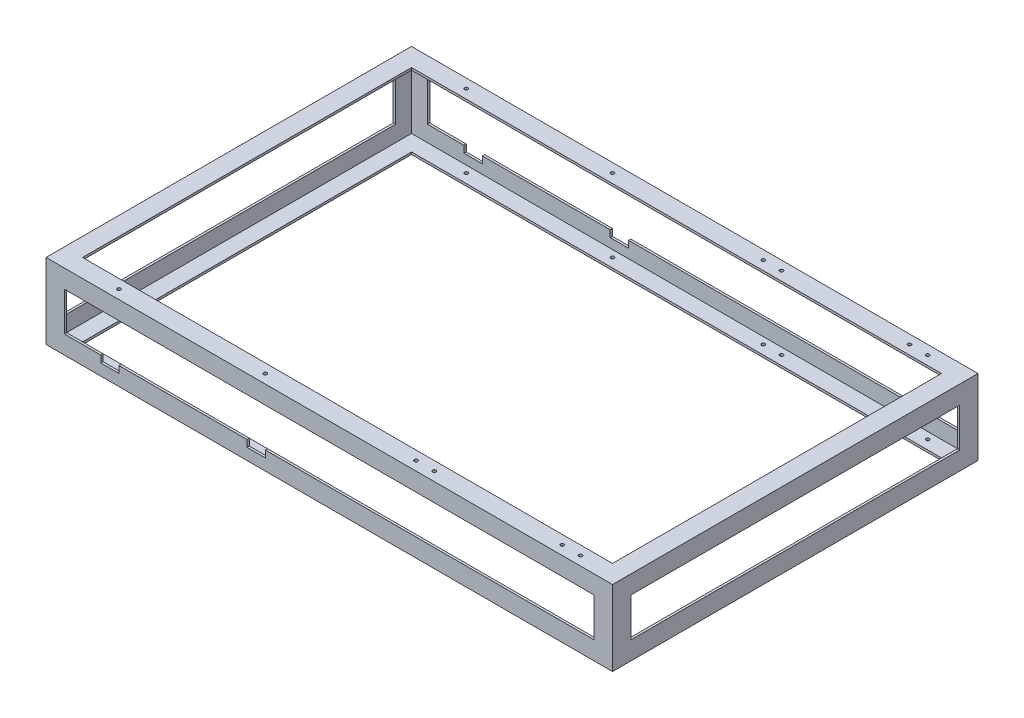
SolidWorks part; units mm, degrees
material "6061 Alloy"
ref_plane "Front Plane" through (0, 0, 0) normal (0, 0, 1) x (1, 0, 0)
ref_plane "Top Plane" through (0, 0, 0) normal (0, 1, 0) x (1, 0, 0)
ref_plane "Right Plane" through (0, 0, 0) normal (1, 0, 0) x (0, 0, -1)
other "Center of Mass"
sketch "Sketch2" plane through (0, 0, 0) normal (1, 0, 0) x (0, 0, -1)
  line L0 (-504.825, -346.075) -> (-504.825, -422.275)
  line L1 (504.825, -422.275) -> (-504.825, -422.275) construction
  line L2 (504.825, -422.275) -> (504.825, 422.275) construction
  line L3 (504.825, 422.275) -> (-504.825, 422.275) construction
  line L4 (-504.825, -422.275) -> (-504.825, 422.275) construction
  line L5 (504.825, -422.275) -> (-504.825, 422.275) construction
  line L6 (504.825, 422.275) -> (-504.825, -422.275) construction
  line L7 (-504.825, -422.275) -> (-428.625, -422.275)
  line L8 (-428.625, -422.275) -> (-428.625, -417.195)
  line L9 (-428.625, -417.195) -> (-498.7519, -417.195)
  line L10 (-498.7519, -417.195) -> (-498.7519, -346.075)
  line L11 (-498.7519, -346.075) -> (-504.825, -346.075)
  line L12 (0, 0) -> (0, -148.4726) construction
  line L13 (0, 0) -> (158.633, 0) construction
  line L14 (498.7519, -417.195) -> (498.7519, -346.075)
  line L15 (428.625, -417.195) -> (498.7519, -417.195)
  line L16 (428.625, -422.275) -> (428.625, -417.195)
  line L17 (504.825, -422.275) -> (428.625, -422.275)
  line L18 (504.825, -346.075) -> (504.825, -422.275)
  line L19 (498.7519, -346.075) -> (504.825, -346.075)
  line L20 (428.625, 417.195) -> (498.7519, 417.195)
  line L21 (428.625, 422.275) -> (428.625, 417.195)
  line L22 (504.825, 422.275) -> (428.625, 422.275)
  line L23 (504.825, 346.075) -> (504.825, 422.275)
  line L24 (498.7519, 346.075) -> (504.825, 346.075)
  line L25 (498.7519, 417.195) -> (498.7519, 346.075)
  line L26 (-498.7519, 417.195) -> (-498.7519, 346.075)
  line L27 (-428.625, 417.195) -> (-498.7519, 417.195)
  line L28 (-428.625, 422.275) -> (-428.625, 417.195)
  line L29 (-504.825, 422.275) -> (-428.625, 422.275)
  line L30 (-504.825, 346.075) -> (-504.825, 422.275)
  line L31 (-498.7519, 346.075) -> (-504.825, 346.075)
  point P0 (0, 0)
  dimension "D1" = 1009.65
  dimension "D2" = 844.55
  dimension "D3" = 76.2
  dimension "D4" = 5.08
extrude "OAL Lenth" [suppressed] add sketch "Sketch2" along normal blind 1574.8
sketch "Sketch3" [suppressed] plane through (0, 0, 0) normal (0, 0, 1) x (1, 0, 0)
  line L0 (0, -422.275) -> (0, -346.075)
  line L1 (1574.8, -346.075) -> (0, -346.075) construction
  line L2 (0, -346.075) -> (0, -422.275) construction
  line L3 (0, -346.075) -> (5.08, -346.075)
  line L4 (5.08, -346.075) -> (5.08, -417.195)
  line L5 (5.08, -417.195) -> (76.2, -417.195)
  line L6 (76.2, -417.195) -> (76.2, -422.275)
  line L7 (1574.8, -422.275) -> (0, -422.275) construction
  line L8 (76.2, -422.275) -> (0, -422.275)
  line L9 (0, 0) -> (697.1877, 0) construction
  line L10 (787.4, 346.075) -> (787.4, -346.075) construction
  line L11 (1574.8, 346.075) -> (0, 346.075) construction
  line L12 (76.2, 422.275) -> (0, 422.275)
  line L13 (76.2, 417.195) -> (76.2, 422.275)
  line L14 (5.08, 417.195) -> (76.2, 417.195)
  line L15 (5.08, 346.075) -> (5.08, 417.195)
  line L16 (0, 346.075) -> (5.08, 346.075)
  line L17 (0, 422.275) -> (0, 346.075)
  line L18 (1574.8, 422.275) -> (1574.8, 346.075)
  line L19 (1574.8, 346.075) -> (1569.72, 346.075)
  line L20 (1569.72, 346.075) -> (1569.72, 417.195)
  line L21 (1569.72, 417.195) -> (1498.6, 417.195)
  line L22 (1498.6, 417.195) -> (1498.6, 422.275)
  line L23 (1498.6, 422.275) -> (1574.8, 422.275)
  line L24 (1498.6, -422.275) -> (1574.8, -422.275)
  line L25 (1498.6, -417.195) -> (1498.6, -422.275)
  line L26 (1569.72, -417.195) -> (1498.6, -417.195)
  line L27 (1569.72, -346.075) -> (1569.72, -417.195)
  line L28 (1574.8, -346.075) -> (1569.72, -346.075)
  line L29 (1574.8, -422.275) -> (1574.8, -346.075)
  dimension "D1" = 5.08
extrude "OAL Width" [suppressed] add sketch "Sketch3" along normal up to surface and the other way up to surface
sketch "Sketch4" [suppressed] plane through (0, 422.275, 0) normal (0, 1, 0) x (1, 0, 0)
  line L0 (0, 504.825) -> (0, 428.625)
  line L1 (0, -428.625) -> (0, -504.825) construction
  line L2 (0, 428.625) -> (5.08, 428.625)
  line L3 (5.08, 428.625) -> (5.08, 499.745)
  line L4 (5.08, 499.745) -> (76.2, 499.745)
  line L5 (76.2, 499.745) -> (76.2, 504.825)
  line L6 (0, 504.825) -> (1574.8, 504.825) construction
  line L7 (76.2, 504.825) -> (0, 504.825)
  line L8 (0, 0) -> (1574.8, 0) construction
  line L9 (1574.8, -428.625) -> (1574.8, -504.825) construction
  line L10 (787.4, 0) -> (787.4, 504.825) construction
  line L11 (76.2, -504.825) -> (0, -504.825)
  line L12 (76.2, -499.745) -> (76.2, -504.825)
  line L13 (5.08, -499.745) -> (76.2, -499.745)
  line L14 (5.08, -428.625) -> (5.08, -499.745)
  line L15 (0, -428.625) -> (5.08, -428.625)
  line L16 (0, -504.825) -> (0, -428.625)
  line L17 (1574.8, -504.825) -> (1574.8, -428.625)
  line L18 (1574.8, -428.625) -> (1569.72, -428.625)
  line L19 (1569.72, -428.625) -> (1569.72, -499.745)
  line L20 (1569.72, -499.745) -> (1498.6, -499.745)
  line L21 (1498.6, -499.745) -> (1498.6, -504.825)
  line L22 (1498.6, -504.825) -> (1574.8, -504.825)
  line L23 (1498.6, 504.825) -> (1574.8, 504.825)
  line L24 (1498.6, 499.745) -> (1498.6, 504.825)
  line L25 (1569.72, 499.745) -> (1498.6, 499.745)
  line L26 (1569.72, 428.625) -> (1569.72, 499.745)
  line L27 (1574.8, 428.625) -> (1569.72, 428.625)
  line L28 (1574.8, 504.825) -> (1574.8, 428.625)
  dimension "D1" = 5.08
  dimension "D2" = 76.2
extrude "OAL Height" [suppressed] add sketch "Sketch4" against normal through all
sketch "Sketch5" plane through (0, 0, 0) normal (1, 0, 0) x (0, 0, -1)
  line L0 (0, 304.8) -> (0, -304.8) construction
  line L1 (-508, -304.8) -> (508, -304.8) construction
  line L2 (-508, -304.8) -> (-508, -254)
  line L3 (-508, -304.8) -> (-457.2, -304.8)
  line L4 (-457.2, -304.8) -> (-457.2, -298.45)
  line L5 (-457.2, -298.45) -> (-501.65, -298.45)
  line L6 (-501.65, -298.45) -> (-501.65, -254)
  line L7 (-501.65, -254) -> (-508, -254)
  line L8 (501.65, -254) -> (508, -254)
  line L9 (501.65, -298.45) -> (501.65, -254)
  line L10 (457.2, -298.45) -> (501.65, -298.45)
  line L11 (457.2, -304.8) -> (457.2, -298.45)
  line L12 (508, -304.8) -> (457.2, -304.8)
  line L13 (508, -304.8) -> (508, -254)
  line L14 (0, -200.025) -> (-176.3903, -200.025) construction
  line L15 (-508, -95.25) -> (508, -95.25) construction
  line L16 (508, -95.25) -> (508, -146.05)
  line L17 (508, -95.25) -> (457.2, -95.25)
  line L18 (457.2, -95.25) -> (457.2, -101.6)
  line L19 (457.2, -101.6) -> (501.65, -101.6)
  line L20 (501.65, -101.6) -> (501.65, -146.05)
  line L21 (501.65, -146.05) -> (508, -146.05)
  line L22 (-501.65, -146.05) -> (-508, -146.05)
  line L23 (-501.65, -101.6) -> (-501.65, -146.05)
  line L24 (-457.2, -101.6) -> (-501.65, -101.6)
  line L25 (-457.2, -95.25) -> (-457.2, -101.6)
  line L26 (-508, -95.25) -> (-457.2, -95.25)
  line L27 (-508, -95.25) -> (-508, -146.05)
  point P4 (0, 0)
  point P8 (0, -304.8)
  point P32 (0, -95.25)
  dimension "D1" = 1016
  dimension "D2" = 609.6
  dimension "D3" = 50.8
  dimension "D4" = 6.35
  dimension "D5" = 104.775
extrude "X Angle Lenth" add sketch "Sketch5" along normal blind 1574.8 separate body
sketch "Sketch6" plane through (0, -304.8, 0) normal (0, -1, 0) x (1, 0, 0)
  line L0 (0, 0) -> (1574.8, 0) construction
  line L1 (1574.8, -508) -> (1574.8, 508) construction
  line L2 (1574.8, -508) -> (1524, -508)
  line L3 (1574.8, -508) -> (1574.8, -457.2)
  line L4 (1574.8, -457.2) -> (1568.45, -457.2)
  line L5 (1568.45, -457.2) -> (1568.45, -501.65)
  line L6 (1568.45, -501.65) -> (1524, -501.65)
  line L7 (1524, -501.65) -> (1524, -508)
  line L8 (1524, 501.65) -> (1524, 508)
  line L9 (1568.45, 501.65) -> (1524, 501.65)
  line L10 (1568.45, 457.2) -> (1568.45, 501.65)
  line L11 (1574.8, 457.2) -> (1568.45, 457.2)
  line L12 (1574.8, 508) -> (1574.8, 457.2)
  line L13 (1574.8, 508) -> (1524, 508)
  line L15 (787.4, 0) -> (787.4, 197.6325) construction
  line L16 (0, -508) -> (0, 508) construction
  line L17 (0, 508) -> (50.8, 508)
  line L18 (0, 508) -> (0, 457.2)
  line L19 (0, 457.2) -> (6.35, 457.2)
  line L20 (6.35, 457.2) -> (6.35, 501.65)
  line L21 (6.35, 501.65) -> (50.8, 501.65)
  line L22 (50.8, 501.65) -> (50.8, 508)
  line L23 (50.8, -501.65) -> (50.8, -508)
  line L24 (6.35, -501.65) -> (50.8, -501.65)
  line L25 (6.35, -457.2) -> (6.35, -501.65)
  line L26 (0, -457.2) -> (6.35, -457.2)
  line L27 (0, -508) -> (0, -457.2)
  line L28 (0, -508) -> (50.8, -508)
  point P3 (787.4, 0)
  point P6 (1574.8, 0)
  point P32 (0, 0)
  dimension "D1" = 50.8
  dimension "D2" = 6.35
  dimension "D3" = 1016
  dimension "D4" = 1574.8
extrude "Y Angle Lenth" add sketch "Sketch6" against normal blind 209.55
sketch "Sketch15" plane through (0, 0, 0) normal (0, 0, 1) x (1, 0, 0)
  line L0 (0, -254) -> (0, -304.8)
  line L1 (0, -95.25) -> (1574.8, -95.25) construction
  line L2 (787.4, -95.25) -> (787.4, 43.9233) construction
  line L3 (1568.45, -254) -> (1574.8, -254)
  line L4 (1568.45, -298.45) -> (1568.45, -254)
  line L5 (1524, -298.45) -> (1568.45, -298.45)
  line L6 (1524, -304.8) -> (1524, -298.45)
  line L7 (0, -304.8) -> (50.8, -304.8)
  line L8 (50.8, -304.8) -> (50.8, -298.45)
  line L9 (50.8, -298.45) -> (6.35, -298.45)
  line L10 (6.35, -298.45) -> (6.35, -254)
  line L11 (6.35, -254) -> (0, -254)
  line L12 (1574.8, -304.8) -> (1524, -304.8)
  line L13 (1574.8, -254) -> (1574.8, -304.8)
  line L20 (787.4, -95.25) -> (787.4, -304.8) construction
  line L21 (1574.8, -304.8) -> (0, -304.8) construction
  line L24 (787.4, -200.025) -> (896.4031, -200.025) construction
  line L27 (1574.8, -146.05) -> (1574.8, -95.25)
  line L28 (1574.8, -95.25) -> (1524, -95.25)
  line L29 (1524, -95.25) -> (1524, -101.6)
  line L30 (1524, -101.6) -> (1568.45, -101.6)
  line L31 (1568.45, -101.6) -> (1568.45, -146.05)
  line L32 (1568.45, -146.05) -> (1574.8, -146.05)
  line L33 (18.8814, -200.025) -> (113.1502, -200.025) construction
  line L35 (6.35, -146.05) -> (0, -146.05)
  line L36 (6.35, -101.6) -> (6.35, -146.05)
  line L37 (50.8, -101.6) -> (6.35, -101.6)
  line L38 (50.8, -95.25) -> (50.8, -101.6)
  line L39 (0, -95.25) -> (50.8, -95.25)
  line L40 (0, -146.05) -> (0, -95.25)
  dimension "D1" = 50.8
  dimension "D2" = 6.35
extrude "Z Angle Lenth" add sketch "Sketch15" against normal up to surface and the other way up to surface
sketch "Sketch16" plane through (0, -95.25, 0) normal (0, 1, 0) x (1, 0, 0)
  line L0 (1409.7, 0) -> (1409.7, 482.6) construction
  line L1 (0, 508) -> (0, -508) construction
  line L2 (1003.3, 0) -> (1003.3, 482.6) construction
  line L3 (584.2, 0) -> (584.2, 482.6) construction
  line L4 (177.8, 0) -> (177.8, 482.6) construction
  line L5 (177.8, 482.6) -> (584.2, 482.6) construction
  line L6 (584.2, 482.6) -> (1003.3, 482.6) construction
  line L7 (1003.3, 482.6) -> (1409.7, 482.6) construction
  line L8 (1409.7, 0) -> (0, 0) construction
  line L9 (1003.3, -482.6) -> (1409.7, -482.6) construction
  line L10 (584.2, -482.6) -> (1003.3, -482.6) construction
  line L11 (177.8, -482.6) -> (584.2, -482.6) construction
  line L12 (0, 508) -> (1574.8, 508) construction
  line L13 (1003.3, 482.6) -> (1054.1, 482.6) construction
  line L14 (1409.7, 482.6) -> (1460.5, 482.6) construction
  line L15 (1003.3, 482.6) -> (1003.3, 498.1872) construction
  line L16 (1003.3, 498.1872) -> (1054.1, 498.1872) construction
  line L17 (1054.1, 498.1872) -> (1054.1, 482.6) construction
  circle A0 centre (1409.7, 482.6) radius 4.7625
  circle A1 centre (1003.3, 482.6) radius 4.7625
  circle A2 centre (584.2, 482.6) radius 4.7625
  circle A3 centre (177.8, 482.6) radius 4.7625
  circle A4 centre (177.8, -482.6) radius 4.7625
  circle A5 centre (584.2, -482.6) radius 4.7625
  circle A6 centre (1003.3, -482.6) radius 4.7625
  circle A7 centre (1409.7, -482.6) radius 4.7625
  circle A8 centre (1054.1, 482.6) radius 4.7625
  circle A9 centre (1460.5, 482.6) radius 4.7625
  circle A10 centre (1460.5, -482.6) radius 4.7625
  circle A11 centre (1054.1, -482.6) radius 4.7625
  dimension "D1" = 9.525
  dimension "D7" = 50.8
  dimension "D2" = 177.8
  dimension "D3" = 406.4
  dimension "D4" = 406.4
  dimension "D5" = 419.1
  dimension "D6" = 25.4
extrude "Wheel Mount LOC Holes" cut sketch "Sketch16" against normal through all
sketch "Sketch17" plane through (0, 0, 508) normal (0, 0, 1) x (1, 0, 0)
  line L0 (1524, -254) -> (50.8, -254) construction
  line L1 (203.2, -273.05) -> (152.4, -273.05)
  line L2 (203.2, -273.05) -> (203.2, -234.95)
  line L3 (203.2, -234.95) -> (152.4, -234.95)
  line L4 (152.4, -273.05) -> (152.4, -234.95)
  line L5 (203.2, -273.05) -> (152.4, -234.95) construction
  line L6 (203.2, -234.95) -> (152.4, -273.05) construction
  line L7 (0, -95.25) -> (0, -304.8) construction
  line L8 (609.6, -273.05) -> (609.6, -234.95)
  line L9 (609.6, -273.05) -> (558.8, -273.05)
  line L10 (558.8, -273.05) -> (558.8, -234.95)
  line L11 (609.6, -234.95) -> (558.8, -234.95)
  point P0 (177.8, -254)
  dimension "D1" = 50.8
  dimension "D2" = 19.05
  dimension "D3" = 177.8
  dimension "D4" = 2
extrude "Front Control Arm Cutouts" cut sketch "Sketch17" against normal through all
sketch "Sketch18" plane through (0, -95.25, 0) normal (0, 1, 0) x (1, 0, 0)
  line L0 (1003.3, -482.6) -> (1030.6685, -482.6) construction
sketch "Sketch19" plane through (0, -298.45, 0) normal (0, 1, 0) x (1, 0, 0)
  line L0 (736.6, -469.9) -> (772.6, -469.9) construction
  line L1 (50.8, -457.2) -> (1524, -457.2) construction
  line L2 (584.2, -482.6) -> (736.6, -482.6) construction
  line L3 (736.6, -482.6) -> (736.6, -469.9) construction
  circle A0 centre (736.6, -469.9) radius 4
  circle A1 centre (772.6, -469.9) radius 4
  dimension "D1" = 36
  dimension "D2" = 8
  dimension "D3" = 12.7
  dimension "D4" = 152.4
extrude "Cut-Extrude1" cut sketch "Sketch19" against normal through all
